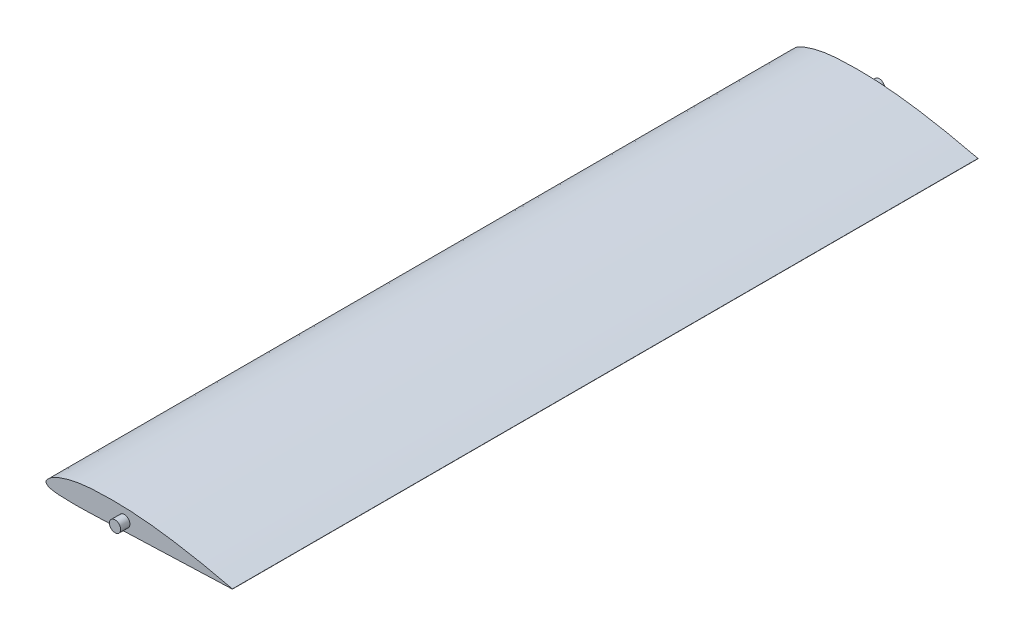
SolidWorks part; units mm, degrees
ref_plane "Front Plane" through (0, 0, 0) normal (0, 0, 1) x (1, 0, 0)
ref_plane "Top Plane" through (0, 0, 0) normal (0, 1, 0) x (1, 0, 0)
ref_plane "Right Plane" through (0, 0, 0) normal (1, 0, 0) x (0, 0, -1)
other "Center of Mass"
curve "Curve2"
  spline degree 3 poles (100, 0.0599, 0) (99.6667, 0.1389, 0) (99.0001, 0.297, 0) (98.0001, 0.5335, 0) (97.0002, 0.7689, 0) (95.6673, 1.0805, 0) (94.0012, 1.464, 0) (92.0011, 1.913, 0) (90.001, 2.3517, 0) (88.001, 2.7804, 0) (86.001, 3.1989, 0) (84.0011, 3.607, 0) (82.0011, 4.0041, 0) (80.0011, 4.3901, 0) (78.001, 4.7646, 0) (76.001, 5.1274, 0) (74.001, 5.4786, 0) (72.001, 5.8178, 0) (70.0009, 6.1451, 0) (68.001, 6.4605, 0) (66.001, 6.7627, 0) (64.0011, 7.0506, 0) (62.0011, 7.3232, 0) (60.0011, 7.5792, 0) (58.001, 7.8174, 0) (56.0009, 8.0377, 0) (54.0009, 8.24, 0) (52.0008, 8.4244, 0) (50.0007, 8.5907, 0) (48.0007, 8.7389, 0) (46.0006, 8.8677, 0) (44.0005, 8.9755, 0) (42.0004, 9.0606, 0) (40.0003, 9.1215, 0) (38.0001, 9.1562, 0) (36, 9.1664, 0) (33.9999, 9.1542, 0) (31.9998, 9.1217, 0) (29.9998, 9.0706, 0) (27.9995, 9.0041, 0) (25.9991, 8.914, 0) (23.9984, 8.7902, 0) (21.9974, 8.623, 0) (19.9961, 8.4023, 0) (17.995, 8.1169, 0) (15.9942, 7.7664, 0) (13.9928, 7.3531, 0) (11.9902, 6.8729, 0) (9.9867, 6.312, 0) (7.9834, 5.6534, 0) (6.3159, 5.0243, 0) (4.987, 4.4324, 0) (3.9799, 3.9169, 0) (2.9638, 3.3042, 0) (2.0257, 2.5894, 0) (1.3212, 1.9111, 0) (0.7834, 1.3659, 0) (0.4419, 0.9673, 0) (0.2174, 0.6242, 0) (0.1075, 0.3995, 0) (0.0374, 0.2059, 0) (-0.0262, -0.0739, 0) (0.0061, -0.365, 0) (0.1075, -0.6183, 0) (0.2162, -0.8198, 0) (0.4373, -1.1135, 0) (0.7742, -1.4249, 0) (1.2999, -1.7806, 0) (2.0457, -2.0688, 0) (2.9972, -2.2604, 0) (3.9964, -2.4592, 0) (4.9972, -2.6119, 0) (6.3307, -2.7532, 0) (7.9992, -2.8493, 0) (9.9993, -2.9441, 0) (11.9997, -3.0014, 0) (13.9999, -3.0284, 0) (16.0001, -3.0291, 0) (18.0001, -3.0079, 0) (20.0002, -2.9688, 0) (22.0002, -2.9162, 0) (24.0001, -2.8531, 0) (26.0001, -2.7824, 0) (28, -2.7072, 0) (30, -2.6305, 0) (32, -2.5554, 0) (34, -2.4816, 0) (36, -2.4086, 0) (38, -2.3361, 0) (40, -2.2635, 0) (42, -2.1905, 0) (44, -2.1171, 0) (46, -2.0436, 0) (48, -1.9699, 0) (50, -1.8962, 0) (52, -1.8226, 0) (54, -1.7491, 0) (56, -1.6757, 0) (58, -1.6023, 0) (60, -1.5289, 0) (62, -1.4555, 0) (64, -1.3821, 0) (66, -1.3086, 0) (68, -1.2351, 0) (70, -1.1617, 0) (72, -1.0882, 0) (74, -1.0148, 0) (76, -0.9413, 0) (78, -0.8679, 0) (80, -0.7944, 0) (82, -0.721, 0) (84, -0.6475, 0) (86, -0.5741, 0) (88, -0.5006, 0) (90, -0.4272, 0) (92, -0.3537, 0) (94, -0.2803, 0) (95.6667, -0.2191, 0) (97, -0.1701, 0) (98, -0.1334, 0) (99, -0.0967, 0) (99.6667, -0.0722, 0) (100, -0.0599, 0) knots 0 0 0 0 0.005028 0.010055 0.015081 0.020105 0.030145 0.040174 0.050191 0.060198 0.070194 0.08018 0.090156 0.100121 0.110076 0.12002 0.129954 0.139879 0.149793 0.159699 0.169594 0.17948 0.189355 0.199219 0.209073 0.218917 0.228751 0.238577 0.248396 0.258207 0.268012 0.277811 0.287604 0.297393 0.307179 0.316964 0.326749 0.336535 0.346322 0.356113 0.365908 0.375711 0.385531 0.395376 0.405259 0.415192 0.425184 0.435248 0.445412 0.455711 0.466191 0.471552 0.477054 0.482787 0.488946 0.494316 0.497126 0.500187 0.502001 0.503128 0.50385 0.50502 0.507318 0.507986 0.509024 0.510668 0.513358 0.515716 0.519949 0.524973 0.529954 0.534903 0.539824 0.54963 0.559425 0.569214 0.579 0.588784 0.59857 0.608356 0.618144 0.627933 0.637724 0.647515 0.657307 0.667099 0.67689 0.686681 0.696472 0.706263 0.716054 0.725846 0.735637 0.745428 0.755219 0.765011 0.774802 0.784593 0.794384 0.804176 0.813967 0.823758 0.833549 0.84334 0.853132 0.862923 0.872714 0.882505 0.892297 0.902088 0.911879 0.92167 0.931461 0.941253 0.951044 0.960835 0.970626 0.980418 0.985313 0.990209 0.995104 1 1 1 1
sketch "Sketch7" plane through (0, 0, 0) normal (0, 0, 1) x (1, 0, 0)
  line L0 (100, 0.0599) -> (100, -0.0599)
  line L1 (0, 0) -> (100, 0) construction
  line L2 (0, 0) -> (0, 2.6099) construction
  spline S1 degree 3 poles (100, 0.0599) (99.6667, 0.1389) (99.0001, 0.297) (98.0003, 0.5335) (97.0004, 0.7689) (95.6676, 1.0804) (94.0016, 1.4639) (92.0016, 1.9129) (90.0017, 2.3515) (88.0018, 2.7802) (86.0019, 3.1987) (83.3368, 3.7424) (79.3412, 4.525) (75.3393, 5.2515) (72.0027, 5.8175) (69.3375, 6.2536) (66.6711, 6.6661) (64.0033, 7.0502) (62.0035, 7.3227) (59.3383, 7.6638) (56.6716, 7.9696) (54.0037, 8.2395) (52.0038, 8.4239) (50.0038, 8.5901) (48.0039, 8.7384) (46.004, 8.8672) (44.0041, 8.9749) (42.0041, 9.06) (40.0041, 9.1209) (38.004, 9.1556) (36.004, 9.1658) (34.004, 9.1536) (32.0041, 9.1211) (30.0041, 9.07) (28.0041, 9.0035) (26.0037, 8.9134) (24.0032, 8.7897) (22.0023, 8.6224) (20.0011, 8.4018) (18.0001, 8.1164) (15.9994, 7.7659) (13.9982, 7.3526) (11.9957, 6.8724) (9.9923, 6.3116) (7.9892, 5.6531) (6.3218, 5.024) (4.993, 4.4322) (3.986, 3.9166) (2.9699, 3.304) (2.0319, 2.5893) (1.3274, 1.911) (0.7897, 1.3658) (0.4482, 0.9672) (0.2237, 0.6241) (0.1138, 0.3995) (0.0436, 0.2059) (-0.0199, -0.0739) (0.0124, -0.3649) (0.1137, -0.6183) (0.2225, -0.8198) (0.4436, -1.1134) (0.7805, -1.4248) (1.306, -1.7805) (2.0518, -2.0687) (3.0033, -2.2602) (4.0025, -2.459) (5.0031, -2.6118) (6.3365, -2.753) (8.0049, -2.8491) (10.005, -2.9439) (12.0052, -3.0012) (14.0053, -3.0283) (16.0053, -3.0289) (18.0053, -3.0077) (20.0052, -2.9686) (22.005, -2.916) (24.6717, -2.8318) (27.338, -2.7326) (30.0044, -2.6304) (32.6708, -2.5303) (35.3374, -2.4327) (38.0039, -2.3359) (40.0038, -2.2633) (42.0036, -2.1903) (44.0035, -2.117) (46.67, -2.0189) (50.0031, -1.896) (53.3363, -1.7735) (56.0028, -1.6756) (58.0026, -1.6022) (60.6691, -1.5044) (63.3356, -1.4065) (66.0021, -1.3085) (68.002, -1.2351) (70.0019, -1.1616) (72.0018, -1.0882) (79.3346, -0.8189) (86.6675, -0.5496) (94.3337, -0.268) (96.3336, -0.1946) (98.3334, -0.1211) (99.3334, -0.0844) (100, -0.0599) knots 0 0 0 0 0.005028 0.010055 0.015081 0.020105 0.030145 0.040174 0.050191 0.060198 0.070194 0.08018 0.100121 0.129954 0.139879 0.149793 0.169594 0.17948 0.189355 0.199219 0.218917 0.228751 0.238577 0.248396 0.258207 0.268012 0.277811 0.287604 0.297393 0.307179 0.316964 0.326749 0.336535 0.346322 0.356113 0.365908 0.375711 0.385531 0.395376 0.405259 0.415192 0.425184 0.435248 0.445412 0.455711 0.466191 0.471552 0.477054 0.482787 0.488946 0.494316 0.497126 0.500187 0.502001 0.503128 0.50385 0.50502 0.507318 0.507986 0.509024 0.510668 0.513358 0.515716 0.519949 0.524973 0.529954 0.534903 0.539824 0.54963 0.559425 0.569214 0.579 0.588784 0.59857 0.608356 0.618144 0.627933 0.647515 0.657307 0.667099 0.686681 0.696472 0.706263 0.716054 0.725846 0.735637 0.755219 0.774802 0.784593 0.794384 0.804176 0.823758 0.833549 0.84334 0.853132 0.862923 0.872714 0.960835 0.970626 0.985313 0.990209 1 1 1 1
  dimension "D1" = 100
extrude "Boss-Extrude4" add sketch "Sketch7" along normal mid plane 400 contours S1 L0
other "Center of Mass Reference Point"
sketch "Sketch8" plane through (0, 0, 0) normal (0, 0, 1) x (1, 0, 0)
  circle A0 centre (42.0369, 2.6692) radius 3
  dimension "D1" = 0
  dimension "D3" = 6
  dimension "D2" = 0
extrude "Boss-Extrude5" add sketch "Sketch8" along normal blind 5 from surface at 200 starting at face at (100, 0.03, 200)
mirror "Mirror1" about plane through (0, 0, 0) normal (0, 0, 1) of "Boss-Extrude5"
